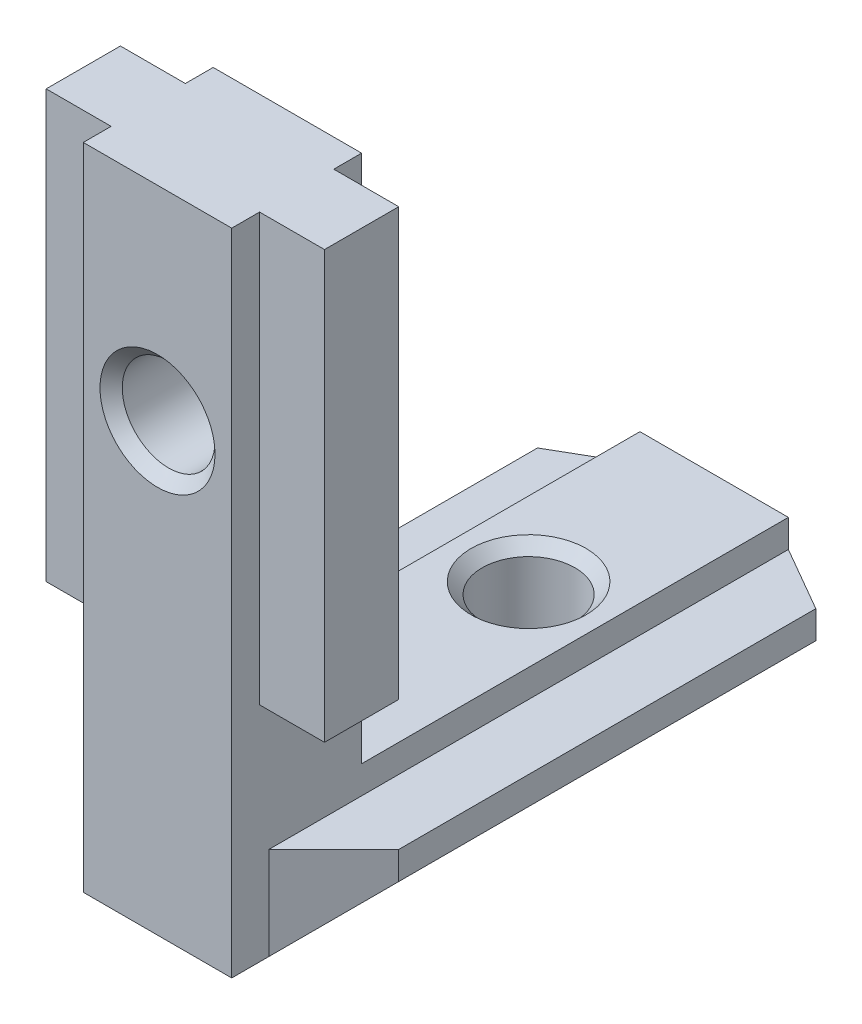
SolidWorks part; units mm, degrees
material "ЦА4М3 ГОСТ 25140-93"
ref_plane "Спереди" through (0, 0, 0) normal (0, 0, 1) x (1, 0, 0)
ref_plane "Сверху" through (0, 0, 0) normal (0, 1, 0) x (1, 0, 0)
ref_plane "Справа" through (0, 0, 0) normal (1, 0, 0) x (0, 0, -1)
sketch "Эскиз1" plane through (0, 0, 0) normal (0, 0, 1) x (1, 0, 0)
  line L0 (4, 0) -> (-4, 0)
  line L1 (-4, 0) -> (-4, -1.5)
  line L2 (-4, -1.5) -> (-7.5, -1.5)
  line L3 (-7.5, -1.5) -> (-7.5, -3)
  line L4 (-4, -6.5) -> (4, -6.5)
  line L5 (0, -6.5) -> (0, 0) construction
  line L7 (4, -1.5) -> (7.5, -1.5)
  line L8 (4, 0) -> (4, -1.5)
  line L9 (-7.5, -3) -> (-4, -6.5)
  line L10 (7.5, -3) -> (4, -6.5)
  line L11 (7.5, -1.5) -> (7.5, -3)
  dimension "D1" = 8
  dimension "D2" = 15
  dimension "D3" = 6.5
  dimension "D4" = 1.5
  dimension "D5" = 1.5
extrude "Бобышка-Вытянуть1" add sketch "Эскиз1" along normal blind 30
sketch "Эскиз2" plane through (0, 0, 0) normal (1, 0, 0) x (0, 0, -1)
  line L0 (-30, -6.5) -> (-30, 28.5)
  line L1 (-30, 28.5) -> (-23, 28.5)
  line L2 (-23, 28.5) -> (-23, -6.5)
  line L4 (-30, -6.5) -> (0, -6.5) construction
  line L5 (-23, -6.5) -> (-30, -6.5)
  dimension "D1" = 35
  dimension "D2" = 7
extrude "Бобышка-Вытянуть2" add sketch "Эскиз2" along normal mid plane 8
sketch "Эскиз3" plane through (0, -1.5, 0) normal (0, 1, 0) x (1, 0, 0)
  line L0 (-4, 0) -> (-7.5, -2.0207)
  line L1 (-7.5, -30) -> (-7.5, 0) construction
  line L2 (-7.5, -2.0207) -> (-7.5, 0)
  line L3 (-7.5, 0) -> (-4, 0)
  line L4 (-4, -28) -> (-7.5, -24.5)
  line L5 (-4, -30) -> (-4, 0) construction
  line L6 (-7.5, -24.5) -> (-7.5, -30)
  line L7 (-4, -30) -> (-7.5, -30) construction
  line L8 (-7.5, -30) -> (-4, -30)
  line L9 (-4, -30) -> (-4, -28)
  line L10 (0, 0) -> (0, -30) construction
  line L11 (4, 0) -> (-4, 0) construction
  line L12 (4, -30) -> (-4, -30) construction
  line L13 (4, -30) -> (4, -28)
  line L14 (7.5, -30) -> (4, -30)
  line L15 (7.5, -24.5) -> (7.5, -30)
  line L16 (4, -28) -> (7.5, -24.5)
  line L17 (7.5, 0) -> (4, 0)
  line L18 (7.5, -2.0207) -> (7.5, 0)
  line L19 (4, 0) -> (7.5, -2.0207)
  dimension "D1" = 2
  dimension "D2" = 45
  dimension "D3" = 30
extrude "Вырез-Вытянуть1" cut sketch "Эскиз3" against normal through all
sketch "Эскиз4" plane through (0, 28.5, 0) normal (0, 1, 0) x (1, 0, 0)
  line L0 (4, -23) -> (4, -30) construction
  line L1 (-7.5, -24.5) -> (7.5, -24.5)
  line L2 (-7.5, -24.5) -> (-7.5, -28.5)
  line L3 (-7.5, -28.5) -> (7.5, -28.5)
  line L4 (7.5, -24.5) -> (7.5, -28.5)
  line L5 (-7.5, -24.5) -> (7.5, -28.5) construction
  line L6 (-7.5, -28.5) -> (7.5, -24.5) construction
  point P0 (0, -26.5)
  point P9 (4, -26.5)
  dimension "D1" = 15
  dimension "D2" = 4
extrude "Бобышка-Вытянуть3" add sketch "Эскиз4" against normal blind 23
hole_wizard "Отверстие обработанное метчиком M61" positions "Эскиз5" profile "Эскиз6" tap size "M6" standard "ISO" end condition through all
sketch "Эскиз5" plane through (0, -6.5, 0) normal (0, -1, 0) x (-1, 0, 0)
  line L0 (4, 0) -> (-4, 0) construction
  point P0 (0, -10)
  dimension "D1" = 10
sketch "Эскиз6" plane through (0, -6.5, 10) normal (1, 0, 0) x (0, 0, -1)
  line L0 (0, 0) -> (0, 6.5)
  line L1 (0, 6.5) -> (3.1, 6.5)
  line L2 (2.5, 5.9) -> (2.5, 0.6)
  line L3 (2.5, 0.6) -> (3.1, 0)
  line L5 (3.1, 0) -> (0, 0)
  line L6 (-2.5, 0.6) -> (-3.1, 0) construction
  line L7 (3.1, 6.5) -> (2.5, 5.9)
  line L8 (-3.1, 6.5) -> (-2.5, 5.9) construction
  line L11 (0, -6.35) -> (0, 107.95) construction
  dimension "Диаметр проходного сверла" = 5
  dimension "Глубина проходного сверла" = 6.5
  dimension "Диаметр передней зенковки" = 6.2
  dimension "Угол передней зенковки" = 90
  dimension "Диаметр задней зенковки" = 6.2
  dimension "Угол задней зенковки" = 90
cosmetic thread "Отверстие резьбы1" parameters "D2"=6
hole_wizard "Отверстие обработанное метчиком M62" positions "Эскиз7" profile "Эскиз8" tap size "M6" standard "ISO" end condition through all
sketch "Эскиз7" plane through (0, 0, 30) normal (0, 0, 1) x (1, 0, 0)
  line L0 (-4, -6.5) -> (4, -6.5) construction
  point P0 (0, 17.5)
  dimension "D1" = 24
sketch "Эскиз8" plane through (0, 17.5, 30) normal (1, 0, 0) x (0, -1, 0)
  line L0 (0, 0) -> (0, 7)
  line L1 (0, 7) -> (3.1, 7)
  line L2 (2.5, 6.4) -> (2.5, 0.6)
  line L3 (2.5, 0.6) -> (3.1, 0)
  line L5 (3.1, 0) -> (0, 0)
  line L6 (-2.5, 0.6) -> (-3.1, 0) construction
  line L7 (3.1, 7) -> (2.5, 6.4)
  line L8 (-3.1, 7) -> (-2.5, 6.4) construction
  line L11 (0, -6.35) -> (0, 107.95) construction
  dimension "Диаметр проходного сверла" = 5
  dimension "Глубина проходного сверла" = 7
  dimension "Диаметр передней зенковки" = 6.2
  dimension "Угол передней зенковки" = 90
  dimension "Диаметр задней зенковки" = 6.2
  dimension "Угол задней зенковки" = 90
cosmetic thread "Отверстие резьбы2" parameters "D2"=6
